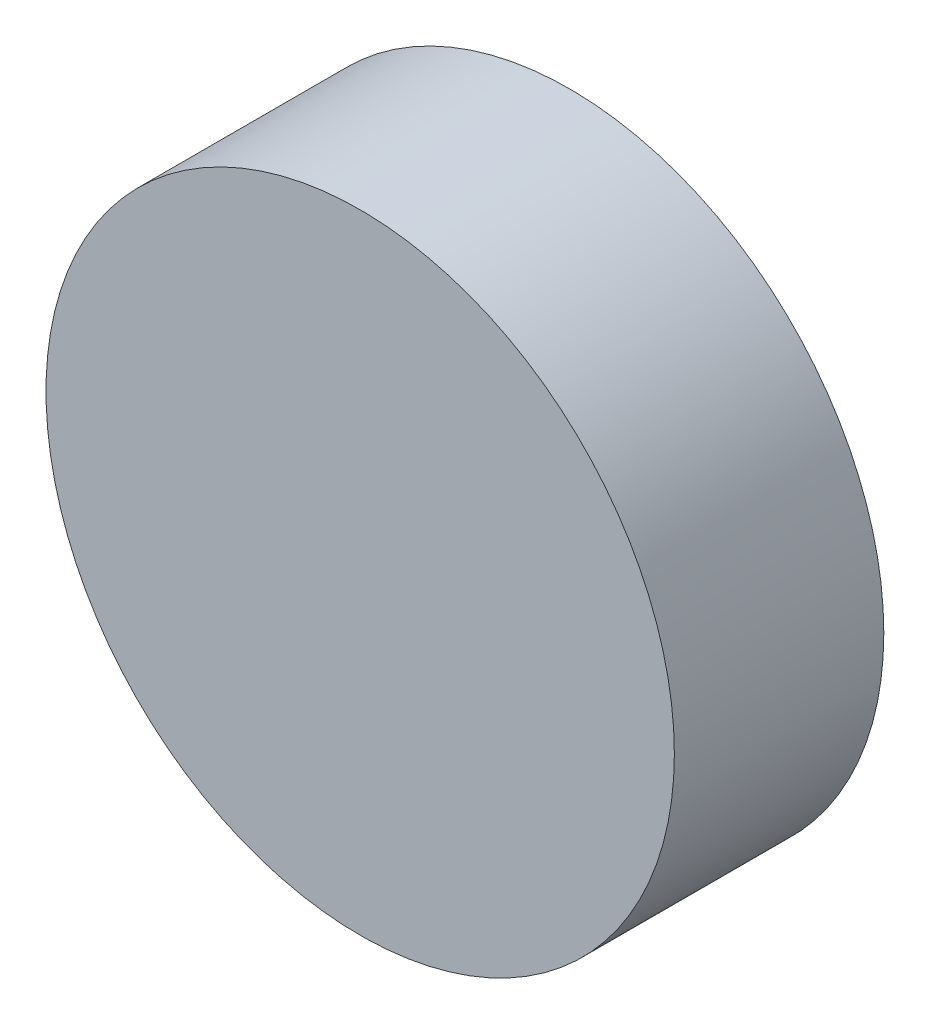
SolidWorks part; units mm, degrees
ref_plane "Front Plane" through (0, 0, 0) normal (0, 0, 1) x (1, 0, 0)
ref_plane "Top Plane" through (0, 0, 0) normal (0, 1, 0) x (1, 0, 0)
ref_plane "Right Plane" through (0, 0, 0) normal (1, 0, 0) x (0, 0, -1)
sketch "MainSketch" plane through (0, 0, 0) normal (0, 0, 1) x (1, 0, 0)
  circle A0 centre (0, 0) radius 38.1
  dimension "D1" = 76.2
extrude "Main" add sketch "MainSketch" along normal blind 25.4
